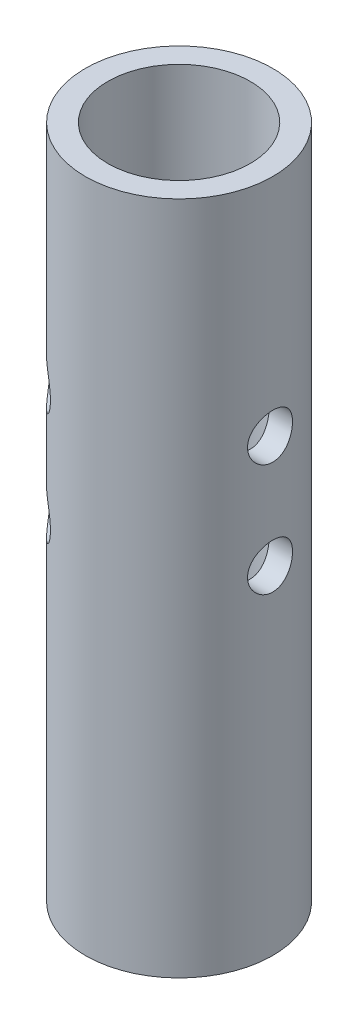
SolidWorks part; units mm, degrees
ref_plane "Front Plane" through (0, 0, 0) normal (0, 0, 1) x (1, 0, 0)
ref_plane "Top Plane" through (0, 0, 0) normal (0, 1, 0) x (1, 0, 0)
ref_plane "Right Plane" through (0, 0, 0) normal (1, 0, 0) x (0, 0, -1)
sketch "Sketch2" plane through (0, 0, 0) normal (0, 1, 0) x (1, 0, 0)
  circle A0 centre (0, 0) radius 12.5
  circle A1 centre (0, 0) radius 9.5
  dimension "D1" = 25
  dimension "D2" = 3
extrude "Boss-Extrude1" add sketch "Sketch2" along normal blind 90
sketch "Sketch3" plane through (0, 0, 0) normal (0, 1, 0) x (1, 0, 0)
  line L0 (0, 0) -> (12.5, 0) construction
  line L1 (0, 0) -> (-8.8388, 8.8388) construction
  line L2 (0, 0) -> (-8.8388, -8.8388) construction
  circle A0 centre (0, 0) radius 12.5 construction
  dimension "D1" = 135
  dimension "D2" = 135
ref_plane "Plane1" through (12.5, 0, 0) normal (1, 0, 0) x (0, 0, -1)
ref_plane "Plane2" through (-8.8388, 0, -8.8388) normal (-0.7071, 0, -0.7071) x (-0.7071, 0, 0.7071)
ref_plane "Plane3" through (-8.8388, 0, 8.8388) normal (-0.7071, 0, 0.7071) x (0.7071, 0, 0.7071)
sketch "Sketch4" plane through (12.5, 0, 0) normal (1, 0, 0) x (0, 0, -1)
  line L0 (0, 0) -> (0, 90) construction
  line L1 (12.5, 90) -> (-12.5, 90) construction
  circle A0 centre (0, 60) radius 3
  circle A1 centre (0, 45) radius 3
  dimension "D1" = 6
  dimension "D2" = 6
  dimension "D3" = 30
  dimension "D4" = 15
extrude "Cut-Extrude1" cut sketch "Sketch4" against normal blind 10
sketch "Sketch5" plane through (-8.8388, 0, -8.8388) normal (-0.7071, 0, -0.7071) x (-0.7071, 0, 0.7071)
  line L0 (0, 0) -> (0, 90) construction
  line L1 (9.5, 90) -> (-9.5, 90) construction
  circle A0 centre (0, 60) radius 3
  circle A1 centre (0, 45) radius 3
  dimension "D1" = 6
  dimension "D2" = 6
  dimension "D3" = 30
  dimension "D4" = 15
extrude "Cut-Extrude2" cut sketch "Sketch5" against normal blind 10
mirror "Mirror1" about plane through (0, 0, 0) normal (0, 0, 1) of "Cut-Extrude2"
